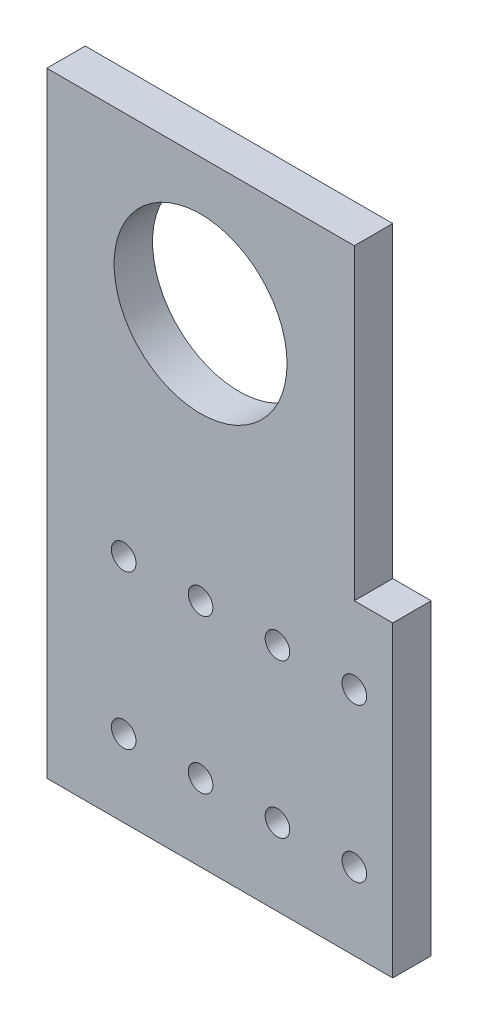
SolidWorks part; units mm, degrees
ref_plane "Front Plane" through (0, 0, 0) normal (0, 0, 1) x (1, 0, 0)
ref_plane "Top Plane" through (0, 0, 0) normal (0, 1, 0) x (1, 0, 0)
ref_plane "Right Plane" through (0, 0, 0) normal (1, 0, 0) x (0, 0, -1)
sketch "Sketch2" plane through (0, 0, 0) normal (0, 0, 1) x (1, 0, 0)
  line L0 (-125.792, -159.6416) -> (-74.992, -159.6416)
  line L11 (-74.992, -159.6416) -> (-68.642, -159.6416)
  line L12 (-68.642, -159.6416) -> (-68.642, -108.8416)
  line L13 (-68.642, -108.8416) -> (-74.992, -108.8416)
  line L14 (-74.992, -58.0416) -> (-74.992, -108.8416)
  line L15 (-125.792, -159.6416) -> (-125.792, -58.0416)
  line L16 (-125.792, -58.0416) -> (-74.992, -58.0416)
  dimension "D1" = 50.8
  dimension "D2" = 101.6
  dimension "D5" = 6.35
  dimension "D6" = 50.8
extrude "Boss-Extrude1" add sketch "Sketch2" along normal blind 6.35
sketch "Sketch3" plane through (0, 0, 6.35) normal (0, 0, 1) x (1, 0, 0)
  circle A0 centre (-100.392, -80.4838) radius 14.2875
  circle A2 centre (-87.692, -146.9416) radius 2.032
  circle A4 centre (-113.092, -146.9416) radius 2.032
  circle A5 centre (-100.392, -146.9416) radius 2.032
  circle A6 centre (-74.992, -146.9416) radius 2.032
  circle A7 centre (-113.092, -121.5416) radius 2.032
  circle A8 centre (-87.692, -121.5416) radius 2.032
  circle A9 centre (-74.992, -121.5416) radius 2.032
  circle A10 centre (-100.392, -121.5416) radius 2.032
  point P2 (-100.392, -44.2513)
  point P5 (-100.392, -80.4838)
  dimension "D1" = 28.575
  dimension "D5" = 4.064
  dimension "D8" = 4.064
  dimension "D9" = 4.064
  dimension "D10" = 4.064
  dimension "D3" = 4.064
  dimension "D7" = 4.064
  dimension "D6" = 4.064
  dimension "D11" = 4.064
  dimension "D2" = 12.7
extrude "Cut-Extrude1" cut sketch "Sketch3" against normal blind 6.35
sketch "Sketch4" plane through (0, 0, 6.35) normal (0, 0, 1) x (1, 0, 0)
  circle A0 centre (-113.092, -146.9416) radius 2.032
  circle A1 centre (-100.392, -146.9416) radius 2.032
  circle A2 centre (-87.692, -146.9416) radius 2.032
  circle A3 centre (-74.992, -146.9416) radius 2.032
